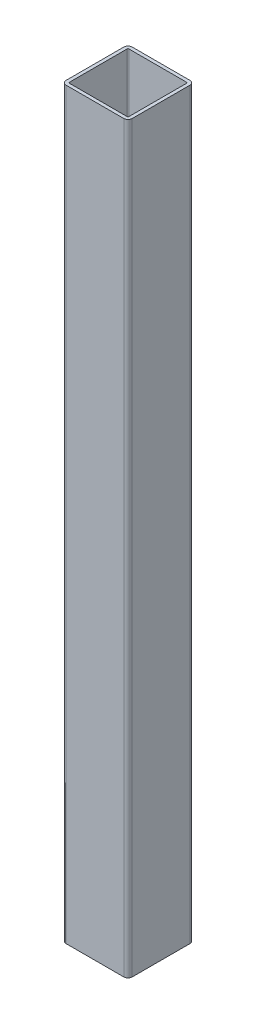
SolidWorks part; units mm, degrees
ref_plane "Спереди" through (0, 0, 0) normal (0, 0, 1) x (1, 0, 0)
ref_plane "Сверху" through (0, 0, 0) normal (0, 1, 0) x (1, 0, 0)
ref_plane "Справа" through (0, 0, 0) normal (1, 0, 0) x (0, 0, -1)
sketch "Эскиз1" plane through (0, 0, 0) normal (0, 1, 0) x (1, 0, 0)
  line L1 (-35, 40) -> (35, 40)
  line L2 (-40, 35) -> (-40, -35)
  line L3 (-35, -40) -> (35, -40)
  line L4 (40, 35) -> (40, -35)
  line L5 (-40, 40) -> (40, -40) construction
  line L6 (-40, -40) -> (40, 40) construction
  arc A0 (-40, -35) -> (-35, -40) centre (-35, -35) ccw
  arc A1 (35, -40) -> (40, -35) centre (35, -35) ccw
  arc A2 (35, 40) -> (40, 35) centre (35, 35) cw
  arc A3 (-35, 40) -> (-40, 35) centre (-35, 35) ccw
  point P0 (0, 0)
  dimension "D1" = 5
extrude "Вытянуть-Тонкостенный1" add sketch "Эскиз1" along normal blind 900 thin
